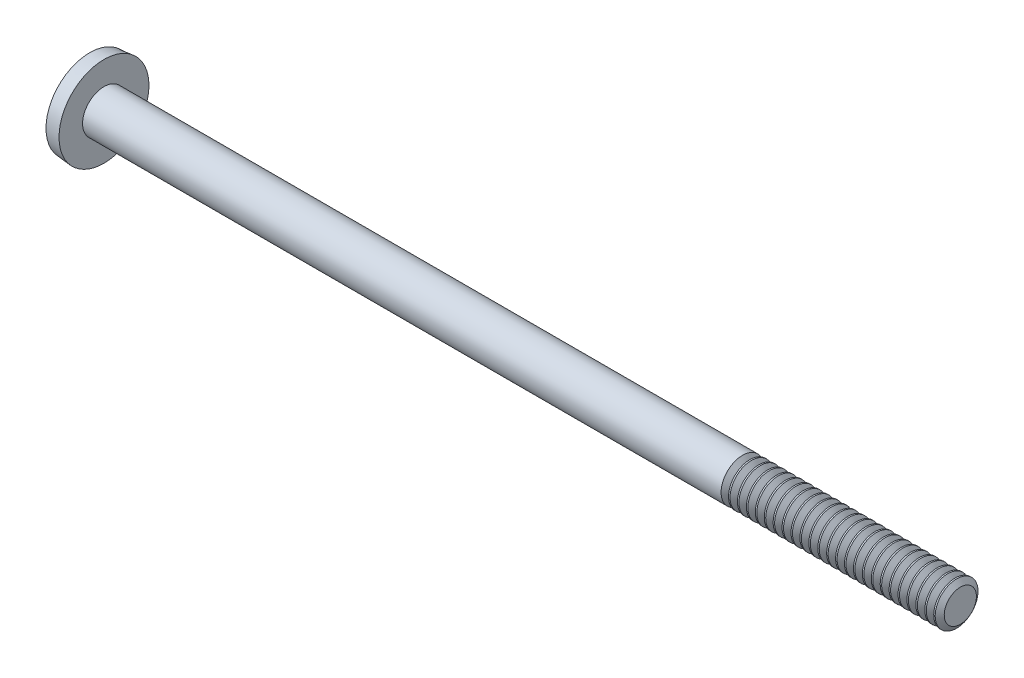
SolidWorks part; units mm, degrees
ref_plane "Plane1" through (0, 0, 0) normal (0, 0, 1) x (1, 0, 0)
ref_plane "Plane2" through (0, 0, 0) normal (0, 1, 0) x (1, 0, 0)
ref_plane "Plane3" through (0, 0, 0) normal (1, 0, 0) x (0, 0, -1)
revolve "Base-Revolve" add sketch "BodySke" angle 360 about L2
sketch "BodySke" plane through (0, 0, 0) normal (0, 0, 1) x (1, 0, 0)
  line L0 (0.8128, 0.762) -> (0.8128, 1.6002)
  line L1 (0.8128, 1.6002) -> (0.3048, 1.5558)
  line L2 (-25.4, 0) -> (127, 0) construction
  line L3 (0.8128, -1.6002) -> (0.3048, -1.5558) construction
  line L4 (0.8128, 0.762) -> (31.2928, 0.762)
  line L5 (31.2928, 0.762) -> (31.2928, 0)
  line L6 (31.2928, 0) -> (0, 0)
  line L7 (0.8128, -0.762) -> (31.2928, -0.762) construction
  line L8 (1.1303, 6.35) -> (1.1303, -3.175) construction
  line L9 (23.6728, 6.35) -> (23.6728, -3.175) construction
  arc A0 (0, 0) -> (0.3048, 1.5558) centre (4.1228, 0) cw
  dimension "Head_ang" = 85
  dimension "Oval_ht" = 0.3048
  dimension "Head_ht" = 0.8128
  dimension "Diameter" = 1.524
  dimension "Length" = 30.48
  dimension "Head_dia" = 3.2004
  dimension "Advance" = 0.3175
  dimension "Thread_nom" = 7.62
cosmetic thread "ThreadCosmetic" parameters "Thread_length"=7.62, "Thread_minor"=1.1455
sketch "Sketch2" plane through (0, 0, 0) normal (1, 0, 0) x (0, 0, -1)
  line L0 (1.6002, -0.2921) -> (1.6002, 0.2921)
  line L1 (1.6002, 0.2921) -> (-1.6002, 0.2921)
  line L2 (-1.6002, 0.2921) -> (-1.6002, -0.2921)
  line L3 (-1.6002, -0.2921) -> (1.6002, -0.2921)
  dimension "D1" = 3.2004
  dimension "D2" = 1.6002
  dimension "D3" = 0.2921
  dimension "Slot_width" = 0.5842
extrude "Slot" cut sketch "Sketch2" along normal blind 0.4572
sketch "Sketch3" plane through (0, 0, 0) normal (1, 0, 0) x (0, 0, -1)
  line L0 (-0.2921, 1.0541) -> (0.2921, 1.0541)
  line L1 (0.2921, 1.0541) -> (0.2921, -1.0541)
  line L2 (0.2921, -1.0541) -> (-0.2921, -1.0541)
  line L3 (-0.2921, -1.0541) -> (-0.2921, 1.0541)
  dimension "D1" = 0.2921
  dimension "Cross_width" = 0.5842
  dimension "D2" = 1.0541
  dimension "Cross_dia" = 2.1082
ref_plane "Plane4" through (1.0668, 0, 0) normal (1, 0, 0) x (0, 0, -1)
sketch "Sketch4" plane through (1.0668, 0, 0) normal (1, 0, 0) x (0, 0, -1)
  line L0 (-0.1461, 0.1461) -> (0.1461, 0.1461)
  line L1 (0.1461, 0.1461) -> (0.1461, -0.1461)
  line L2 (0.1461, -0.1461) -> (-0.1461, -0.1461)
  line L3 (-0.1461, -0.1461) -> (-0.1461, 0.1461)
  dimension "D1" = 0.2921
  dimension "D2" = 0.1461
  dimension "D3" = 0.2921
  dimension "D4" = 0.1461
loft "Cross" cut profiles "Sketch3", "Sketch4"
pattern_circular "CirPattern1" count 2 every 90 about axis through (0, 0, 0) along (1, 0, 0) of "Cross"
sketch "ThdSchSke" plane through (0, 0, 0) normal (0, 0, 1) x (1, 0, 0)
  line L0 (23.6728, -0.5728) -> (23.5403, -0.762)
  line L1 (23.6728, -0.5728) -> (23.8053, -0.762)
  line L2 (23.8053, -0.762) -> (23.8053, -0.9525)
  line L3 (-3.175, 0) -> (5.1513, 0) construction
  line L5 (23.8053, -0.9525) -> (23.5403, -0.9525)
  line L6 (23.5403, -0.9525) -> (23.5403, -0.762)
  dimension "Thread_minor" = 1.1455
  dimension "Diameter" = 1.524
  dimension "Start" = 23.6728
  dimension "SideAngle" = 55
  dimension "VeeAngle" = 70
  dimension "Overcut" = 1.905
revolve "ThreadSchematic" cut sketch "ThdSchSke" angle 360 about L3
pattern_linear "ThdSchPat" count 25 spacing 0.3175 along (1, 0, 0) of "ThreadSchematic"
equation "\"D1@Sketch3\" = \"Cross_width@Sketch3\" / 2"
equation "\"D2@Sketch3\" = \"Cross_dia@Sketch3\" / 2"
equation "\"D1@Sketch4\" = \"Cross_width@Sketch3\"*.5"
equation "\"D2@Sketch4\" = \"D1@Sketch4\" / 2"
equation "\"D3@Sketch4\" = \"D1@Sketch4\""
equation "\"D4@Sketch4\" = \"D2@Sketch4\""
equation "\"D1@Sketch2\" = \"Head_dia@BodySke\""
equation "\"D2@Sketch2\" = \"D1@Sketch2\" / 2"
equation "\"D3@Sketch2\" = \"Slot_width@Sketch2\" / 2"
equation "\"Thread_length@ThreadCosmetic\" = ((sgn( (\"Length@BodySke\" - \"Advance@BodySke\" ) - \"Thread_nom@BodySke\" )-1)*( (\"Length@BodySke\" - \"Advance@BodySke\" ) - \"Thread_nom@BodySke\" ))/-2+ \"Thread_nom@BodySke\""
equation "\"Thread_minor@ThdSchSke\" = \"Thread_minor@ThreadCosmetic\""
equation "\"Diameter@ThdSchSke\" = \"Diameter@BodySke\""
equation "\"Overcut@ThdSchSke\" = \"Diameter@BodySke\" * 1.25"
equation "\"Start@ThdSchSke\" = \"Head_ht@BodySke\" + \"Length@BodySke\" - \"Thread_length@ThreadCosmetic\"  '---Non-countersunk---"
equation "\"Num_threads@ThdSchPat\" = int( \"Thread_length@ThreadCosmetic\" / \"Advance@BodySke\" + 0.999 )  + 1"
equation "\"Advance@ThdSchPat\" = \"Thread_length@ThreadCosmetic\" /  (\"Num_threads@ThdSchPat\" - 1) 'relax it"
